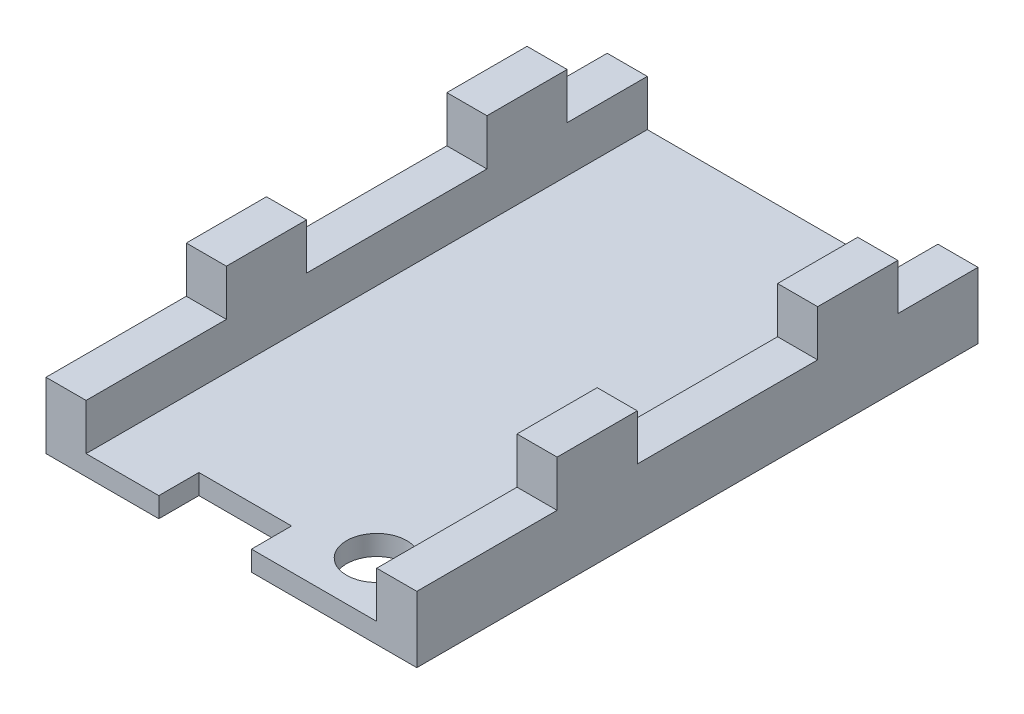
SolidWorks part; units mm, degrees
ref_plane "Front Plane" through (0, 0, 0) normal (0, 0, 1) x (1, 0, 0)
ref_plane "Top Plane" through (0, 0, 0) normal (0, 1, 0) x (1, 0, 0)
ref_plane "Right Plane" through (0, 0, 0) normal (1, 0, 0) x (0, 0, -1)
sketch "main board outline" plane through (0, 0, 0) normal (0, 1, 0) x (1, 0, 0)
  line L1 (-27.2474, 14.651) -> (-12.7474, 14.651)
  line L2 (-27.2474, 14.651) -> (-27.2474, -13.349)
  line L3 (-27.2474, -13.349) -> (-12.7474, -13.349)
  line L4 (-12.7474, 14.651) -> (-12.7474, -13.349)
  line L5 (-29.2474, 14.651) -> (-10.7474, 14.651)
  line L6 (-29.2474, 14.651) -> (-29.2474, -13.349)
  line L7 (-29.2474, -13.349) -> (-10.7474, -13.349)
  line L8 (-10.7474, 14.651) -> (-10.7474, -13.349)
  dimension "D1" = 28
  dimension "D2" = 14.5
  dimension "D3" = 2
  dimension "D4" = 2
extrude "side1" add sketch "main board outline" along normal blind 1 contours L6 L7 L8 L5
sketch "Sketch2" plane through (0, 1, 0) normal (0, 1, 0) x (1, 0, 0)
  line L0 (-29.2474, -13.349) -> (-10.7474, -13.349) construction
  line L1 (-29.2474, 14.651) -> (-27.2474, 14.651)
  line L2 (-29.2474, 14.651) -> (-29.2474, -13.349)
  line L3 (-29.2474, -13.349) -> (-27.2474, -13.349)
  line L4 (-27.2474, 14.651) -> (-27.2474, -13.349)
  line L6 (-10.7474, 14.651) -> (-12.7474, 14.651)
  line L7 (-10.7474, 14.651) -> (-10.7474, -13.349)
  line L8 (-10.7474, -13.349) -> (-12.7474, -13.349)
  line L9 (-12.7474, 14.651) -> (-12.7474, -13.349)
  dimension "D1" = 2
  dimension "D2" = 2
extrude "walls" add sketch "Sketch2" along normal blind 2.3
sketch "Sketch3" plane through (0, 0, 0) normal (0, -1, 0) x (-1, 0, 0)
  line L0 (29.2474, -13.349) -> (10.7474, -13.349) construction
  line L1 (10.7474, 14.651) -> (10.7474, -13.349) construction
  circle A0 centre (15.4906, -10.6058) radius 1.5
  dimension "D1" = 2.7432
  dimension "D2" = 4.7432
extrude "screw hole" cut sketch "Sketch3" against normal blind 2.3
sketch "Sketch4" plane through (0, 0, 0) normal (0, -1, 0) x (-1, 0, 0)
  line L0 (29.2474, -13.349) -> (10.7474, -13.349) construction
  line L1 (18.9958, -13.349) -> (23.6186, -13.349)
  line L2 (18.9958, -13.349) -> (18.9958, -11.349)
  line L3 (18.9958, -11.349) -> (23.6186, -11.349)
  line L4 (23.6186, -13.349) -> (23.6186, -11.349)
  line L5 (10.7474, 14.651) -> (10.7474, -13.349) construction
  dimension "D1" = 8.2484
  dimension "D2" = 12.8712
  dimension "D3" = 2
extrude "Cut-Extrude2" cut sketch "Sketch4" against normal blind 2.3
sketch "Sketch5" plane through (0, 3.3, 0) normal (0, 1, 0) x (1, 0, 0)
  line L0 (-29.2474, 14.651) -> (-29.2474, -13.349) construction
  line L1 (-29.2474, 10.651) -> (-27.2474, 10.651)
  line L2 (-29.2474, 10.651) -> (-29.2474, 6.651)
  line L3 (-29.2474, 6.651) -> (-27.2474, 6.651)
  line L4 (-27.2474, 10.651) -> (-27.2474, 6.651)
  line L5 (-27.2474, -13.349) -> (-27.2474, 14.651) construction
  line L6 (-27.2474, -13.349) -> (-27.2474, 14.651) construction
  line L7 (-29.2474, -2.349) -> (-27.2474, -2.349)
  line L8 (-29.2474, -2.349) -> (-29.2474, -6.349)
  line L9 (-29.2474, -6.349) -> (-27.2474, -6.349)
  line L10 (-27.2474, -2.349) -> (-27.2474, -6.349)
  line L11 (-12.7474, 14.651) -> (-12.7474, -13.349) construction
  line L12 (-12.7474, 10.651) -> (-10.7474, 10.651)
  line L13 (-12.7474, 10.651) -> (-12.7474, 6.651)
  line L14 (-12.7474, 6.651) -> (-10.7474, 6.651)
  line L15 (-10.7474, 10.651) -> (-10.7474, 6.651)
  line L16 (-10.7474, -13.349) -> (-10.7474, 14.651) construction
  line L18 (-12.7474, -2.349) -> (-10.7474, -2.349)
  line L19 (-12.7474, -2.349) -> (-12.7474, -6.349)
  line L20 (-12.7474, -6.349) -> (-10.7474, -6.349)
  line L21 (-10.7474, -2.349) -> (-10.7474, -6.349)
  line L22 (-27.2474, 14.651) -> (-29.2474, 14.651) construction
  line L23 (-10.7474, 14.651) -> (-12.7474, 14.651) construction
  line L24 (-29.2474, -13.349) -> (-27.2474, -13.349) construction
  line L25 (-12.7474, -13.349) -> (-10.7474, -13.349) construction
  point P28 (-11.7474, 14.651)
  dimension "D1" = 4
  dimension "D2" = 4
  dimension "D3" = 4
  dimension "D4" = 4
  dimension "D5" = 4
  dimension "D6" = 4
  dimension "D7" = 7
  dimension "D8" = 7
extrude "Boss-Extrude3" add sketch "Sketch5" along normal blind 2.3
